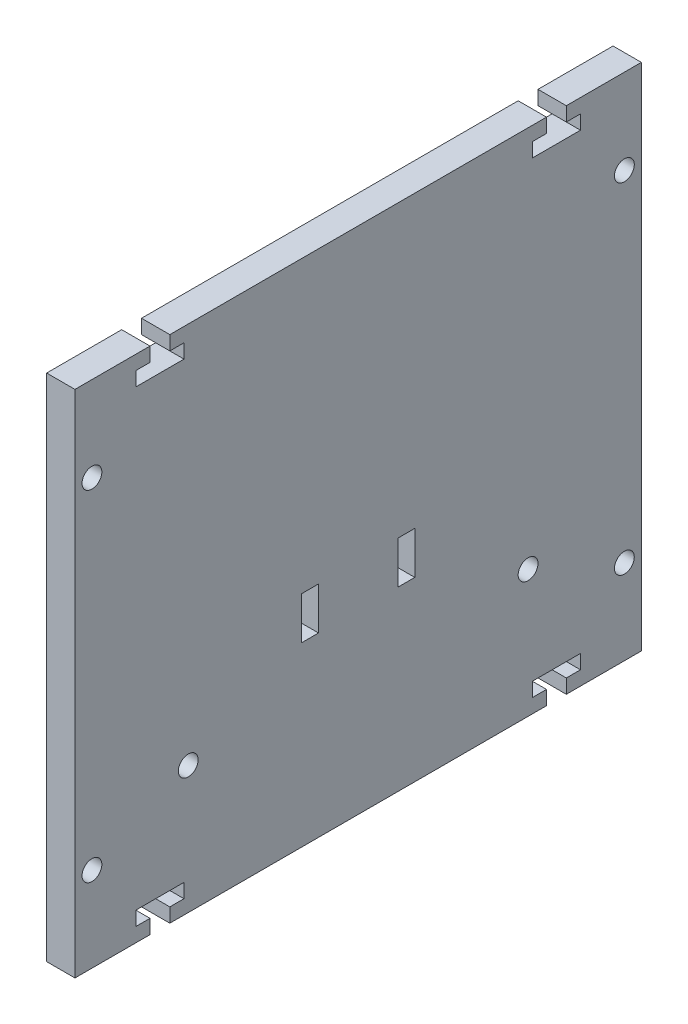
SolidWorks part; units mm, degrees
ref_plane "Спереди" through (0, 0, 0) normal (0, 0, 1) x (1, 0, 0)
ref_plane "Сверху" through (0, 0, 0) normal (0, 1, 0) x (1, 0, 0)
ref_plane "Справа" through (0, 0, 0) normal (1, 0, 0) x (0, 0, -1)
sketch "Эскиз1" plane through (0, 0, 0) normal (1, 0, 0) x (0, 0, -1)
  line L0 (-36.75, 45) -> (-36.75, 42.5)
  line L1 (-50, -45) -> (-36.75, -45)
  line L2 (-50, -45) -> (-50, 45)
  line L3 (-50, 45) -> (-36.75, 45)
  line L4 (50, -45) -> (50, 45)
  line L5 (-50, -45) -> (50, 45) construction
  line L6 (-50, 45) -> (50, -45) construction
  line L7 (-36.75, 42.5) -> (-39.25, 42.5)
  line L8 (-39.25, 42.5) -> (-39.25, 40)
  line L9 (-39.25, 40) -> (-30.75, 40)
  line L10 (-33.25, 45) -> (33.25, 45)
  line L11 (-30.75, 42.5) -> (-30.75, 40)
  line L12 (-33.25, 42.5) -> (-30.75, 42.5)
  line L13 (-33.25, 45) -> (-33.25, 42.5)
  line L14 (0, 0) -> (0, 21.2721) construction
  line L15 (0, 0) -> (18.8007, 0) construction
  line L16 (33.25, 45) -> (33.25, 42.5)
  line L17 (33.25, 42.5) -> (30.75, 42.5)
  line L18 (30.75, 42.5) -> (30.75, 40)
  line L19 (39.25, 40) -> (30.75, 40)
  line L20 (39.25, 42.5) -> (39.25, 40)
  line L21 (36.75, 42.5) -> (39.25, 42.5)
  line L22 (36.75, 45) -> (36.75, 42.5)
  line L23 (-33.25, -45) -> (-33.25, -42.5)
  line L24 (-33.25, -42.5) -> (-30.75, -42.5)
  line L25 (-30.75, -42.5) -> (-30.75, -40)
  line L26 (-39.25, -40) -> (-30.75, -40)
  line L27 (-39.25, -42.5) -> (-39.25, -40)
  line L28 (-36.75, -42.5) -> (-39.25, -42.5)
  line L29 (-36.75, -45) -> (-36.75, -42.5)
  line L30 (36.75, -45) -> (36.75, -42.5)
  line L31 (36.75, -42.5) -> (39.25, -42.5)
  line L32 (39.25, -42.5) -> (39.25, -40)
  line L33 (39.25, -40) -> (30.75, -40)
  line L34 (30.75, -42.5) -> (30.75, -40)
  line L35 (33.25, -42.5) -> (30.75, -42.5)
  line L36 (33.25, -45) -> (33.25, -42.5)
  line L37 (36.75, 45) -> (50, 45)
  line L38 (36.75, -45) -> (50, -45)
  line L39 (-33.25, -45) -> (33.25, -45)
  line L40 (-13, -23) -> (13, 3) construction
  line L41 (-13, 3) -> (13, 3) construction
  line L42 (13, 3) -> (-13, 3) construction
  line L43 (13, 3) -> (13, -23) construction
  line L44 (13, -23) -> (-13, -23) construction
  line L45 (-13, 3) -> (-13, -23) construction
  line L46 (13, -23) -> (-13, 3) construction
  line L47 (0, -10) -> (0, -23) construction
  line L48 (0, -10) -> (-8.5, -10) construction
  line L49 (10, -6.25) -> (7, -6.25)
  line L50 (-10, -13.75) -> (-7, -13.75)
  line L51 (-10, -13.75) -> (-10, -6.25)
  line L52 (-10, -6.25) -> (-7, -6.25)
  line L53 (-7, -13.75) -> (-7, -6.25)
  line L54 (-10, -13.75) -> (-7, -6.25) construction
  line L55 (-10, -6.25) -> (-7, -13.75) construction
  line L56 (10, -13.75) -> (7, -13.75)
  line L57 (10, -13.75) -> (10, -6.25)
  line L58 (7, -13.75) -> (7, -6.25)
  circle A0 centre (-47, 30) radius 1.75
  circle A1 centre (47, 30) radius 1.75
  circle A2 centre (47, -30) radius 1.75
  circle A3 centre (-47, -30) radius 1.75
  circle A4 centre (-30, -22.5) radius 1.75
  circle A5 centre (30, -22.5) radius 1.75
  point P0 (0, 0)
  point P16 (-37, 42.5)
  point P27 (37, 42.5)
  point P36 (-37, -42.5)
  point P45 (37, -42.5)
  dimension "D10" = 3.5
  dimension "D16" = 3.5
  dimension "D19" = 55
  dimension "D1" = 100
  dimension "D2" = 90
  dimension "D3" = 3.5
  dimension "D4" = 13.25
  dimension "D5" = 2.5
  dimension "D6" = 2.5
  dimension "D7" = 5
  dimension "D8" = 2.5
  dimension "D9" = 8.5
  dimension "D11" = 3
  dimension "D12" = 15
  dimension "D13" = 8.5
  dimension "D14" = 3
  dimension "D15" = 7.5
  dimension "D17" = 20
  dimension "D18" = 67.5
extrude "Бобышка-Вытянуть1" add sketch "Эскиз1" along normal blind 5
